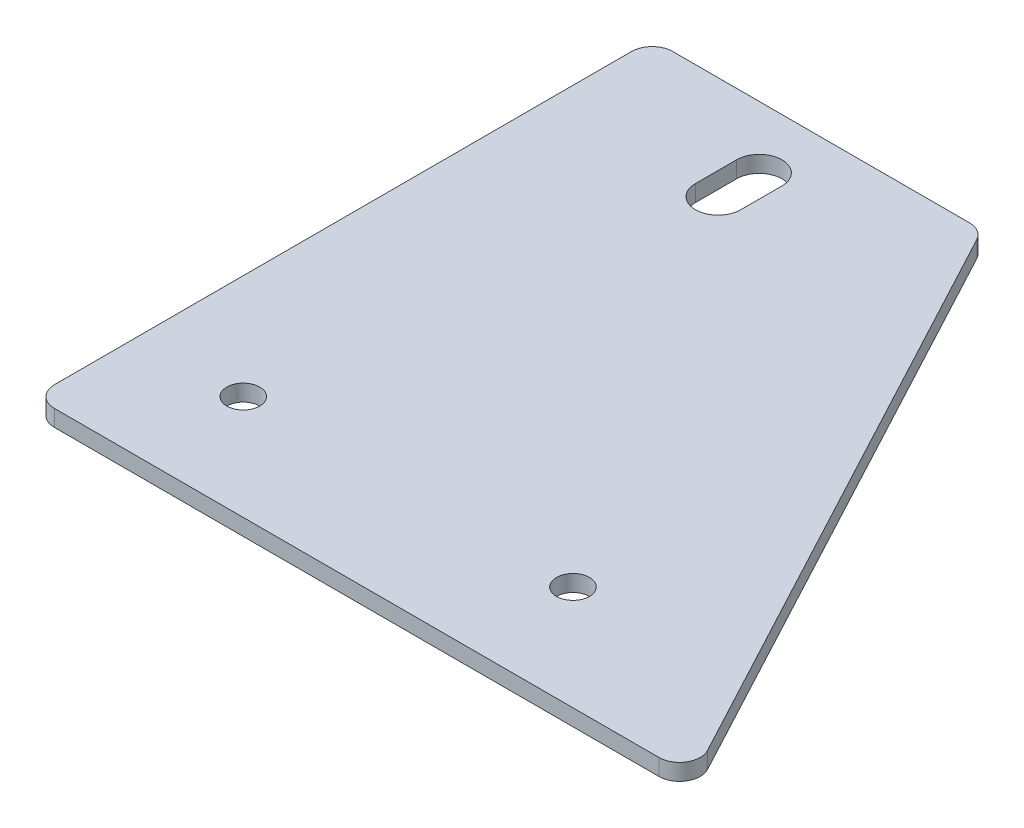
SolidWorks part; units mm, degrees
material "AISI 304"
ref_plane "Front Plane" through (0, 0, 0) normal (0, 0, 1) x (1, 0, 0)
ref_plane "Top Plane" through (0, 0, 0) normal (0, 1, 0) x (1, 0, 0)
ref_plane "Right Plane" through (0, 0, 0) normal (1, 0, 0) x (0, 0, -1)
sketch "Sketch2" plane through (0, 0, 0) normal (0, 1, 0) x (1, 0, 0)
  line L0 (-41, 0) -> (110.6667, 0)
  line L1 (115.0784, 7.3529) -> (40.4118, 147.3529)
  line L2 (36, 150) -> (-36, 150)
  line L3 (-41, 145) -> (-41, 0)
  arc A0 (115.0784, 7.3529) -> (110.6667, 0) centre (110.6667, 5) cw
  arc A1 (40.4118, 147.3529) -> (36, 150) centre (36, 145) ccw
  arc A2 (-36, 150) -> (-41, 145) centre (-36, 145) ccw
  point P3 (0, 150)
  point P8 (119, 0)
  point P11 (39, 150)
  point P14 (-41, 150)
  dimension "D4" = 5
  dimension "D1" = 80
  dimension "D2" = 150
  dimension "D3" = 160
extrude "Boss-Extrude1" add sketch "Sketch2" along normal blind 4 contours L3 L0 A0 L1 A1 L2 A2
sketch "Sketch3" plane through (0, 4, 0) normal (0, 1, 0) x (1, 0, 0)
  line L0 (-41, 145) -> (-41, 0) construction
  line L2 (-41, 0) -> (110.6667, 0) construction
  line L3 (0, 135) -> (0, 125) construction
  line L4 (5.5, 135) -> (5.5, 125)
  line L5 (-5.5, 135) -> (-5.5, 125)
  line L6 (36, 150) -> (-36, 150) construction
  circle A0 centre (-15.6, 25.4) radius 4
  circle A1 centre (64.4, 25.4) radius 4
  arc A3 (5.5, 135) -> (-5.5, 135) centre (0, 135) ccw
  arc A4 (-5.5, 125) -> (5.5, 125) centre (0, 125) ccw
  point P10 (0, 130)
  point P20 (0, 150)
  dimension "D3" = 8
  dimension "D6" = 5.5
  dimension "D1" = 25.4
  dimension "D2" = 25.4
  dimension "D4" = 80
  dimension "D5" = 10
  dimension "D7" = 20
extrude "Cut-Extrude1" cut sketch "Sketch3" against normal through all
fillet "Fillet1" radius 5 1 edges at (-41, 2, 0)
